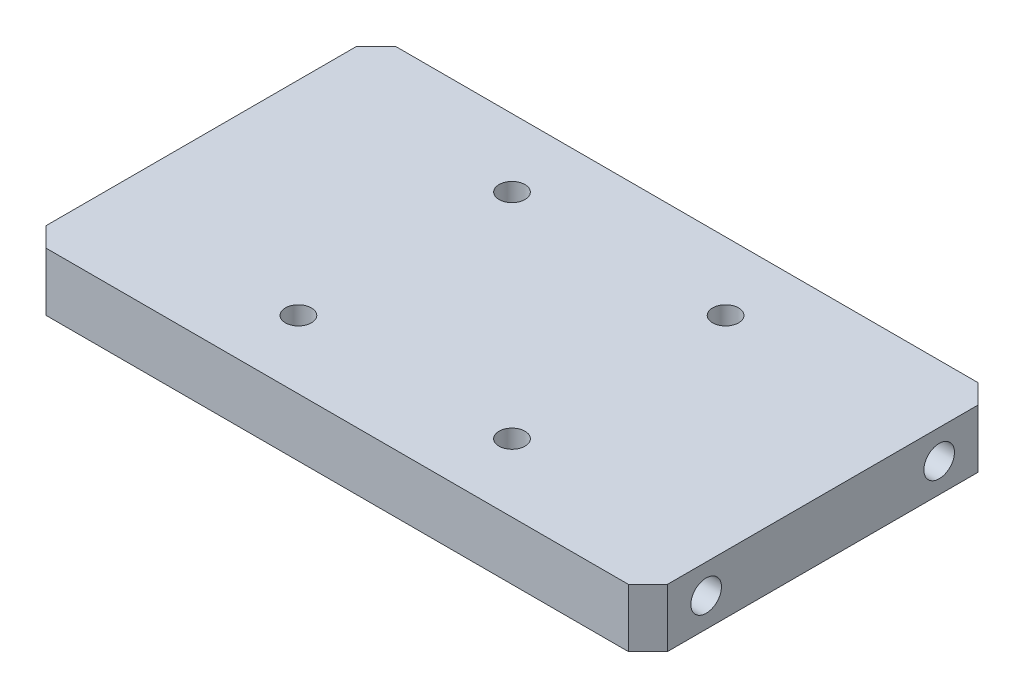
SolidWorks part; units mm, degrees
ref_plane "Front Plane" through (0, 0, 0) normal (0, 0, 1) x (1, 0, 0)
ref_plane "Top Plane" through (0, 0, 0) normal (0, 1, 0) x (1, 0, 0)
ref_plane "Right Plane" through (0, 0, 0) normal (1, 0, 0) x (0, 0, -1)
other "Configuration Table"
sketch "Sketch1" plane through (0, 0, 0) normal (0, 1, 0) x (1, 0, 0)
  line L1 (-101.6, -57.15) -> (101.6, -57.15)
  line L2 (-101.6, -57.15) -> (-101.6, 57.15)
  line L3 (-101.6, 57.15) -> (101.6, 57.15)
  line L4 (101.6, -57.15) -> (101.6, 57.15)
  line L5 (0, 57.15) -> (0, -57.15) construction
  line L6 (-101.6, 0) -> (101.6, 0) construction
  point P317 (0, 0)
  dimension "D1" = 114.3
  dimension "D2" = 203.2
extrude "Boss-Extrude1" add sketch "Sketch1" along normal blind 19.05
sketch "Sketch2" plane through (-101.6, 0, 0) normal (-1, 0, 0) x (0, 0, 1)
  line L0 (0, 0) -> (0, 19.05) construction
  line L1 (-57.15, 0) -> (57.15, 0) construction
  line L2 (-57.15, 19.05) -> (57.15, 19.05) construction
  line L3 (0, 9.525) -> (-57.15, 9.525) construction
  line L4 (-57.15, 19.05) -> (-57.15, 0) construction
  circle A0 centre (-38.1, 9.525) radius 5
  circle A1 centre (38.1, 9.525) radius 5
  dimension "D1" = 10
  dimension "D2" = 19.05
extrude "Cut-Extrude1" cut sketch "Sketch2" against normal blind 19.05
mirror "Mirror1" about plane through (0, 0, 0) normal (1, 0, 0) of "Cut-Extrude1"
chamfer "Chamfer1" distance 6.35 angle 45 4 edges at (101.6, 9.525, -57.15) (101.6, 9.525, 57.15) (-101.6, 9.525, -57.15) (-101.6, 9.525, 57.15)
hole_wizard "M10x1.5 Tapped Hole1" positions "Sketch4" profile "Sketch3" tap size "M10x1.5" standard "ANSI Metric" end condition through all
sketch "Sketch4" plane through (0, 19.05, 0) normal (0, 1, 0) x (1, 0, 0)
  point P0 (34.925, -34.925)
  point P3 (-34.925, -34.925)
  point P6 (34.925, 34.925)
  point P9 (-34.925, 34.925)
sketch "Sketch3" plane through (34.925, 19.05, 34.925) normal (1, 0, 0) x (0, 0, 1)
  line L0 (0, 0) -> (0, 19.05)
  line L1 (0, 19.05) -> (4.25, 19.05)
  line L2 (4.25, 19.05) -> (4.25, 0)
  line L5 (4.25, 0) -> (0, 0)
  line L11 (0, -6.35) -> (0, 107.95) construction
  dimension "Thru Tap Drill Dia." = 8.5
  dimension "Thru Tap Drill Depth" = 19.05
cosmetic thread "Hole Thread1" parameters "D2"=10
cosmetic thread "Hole Thread2" parameters "D2"=10
cosmetic thread "Hole Thread3" parameters "D2"=10
cosmetic thread "Hole Thread4" parameters "D2"=10
